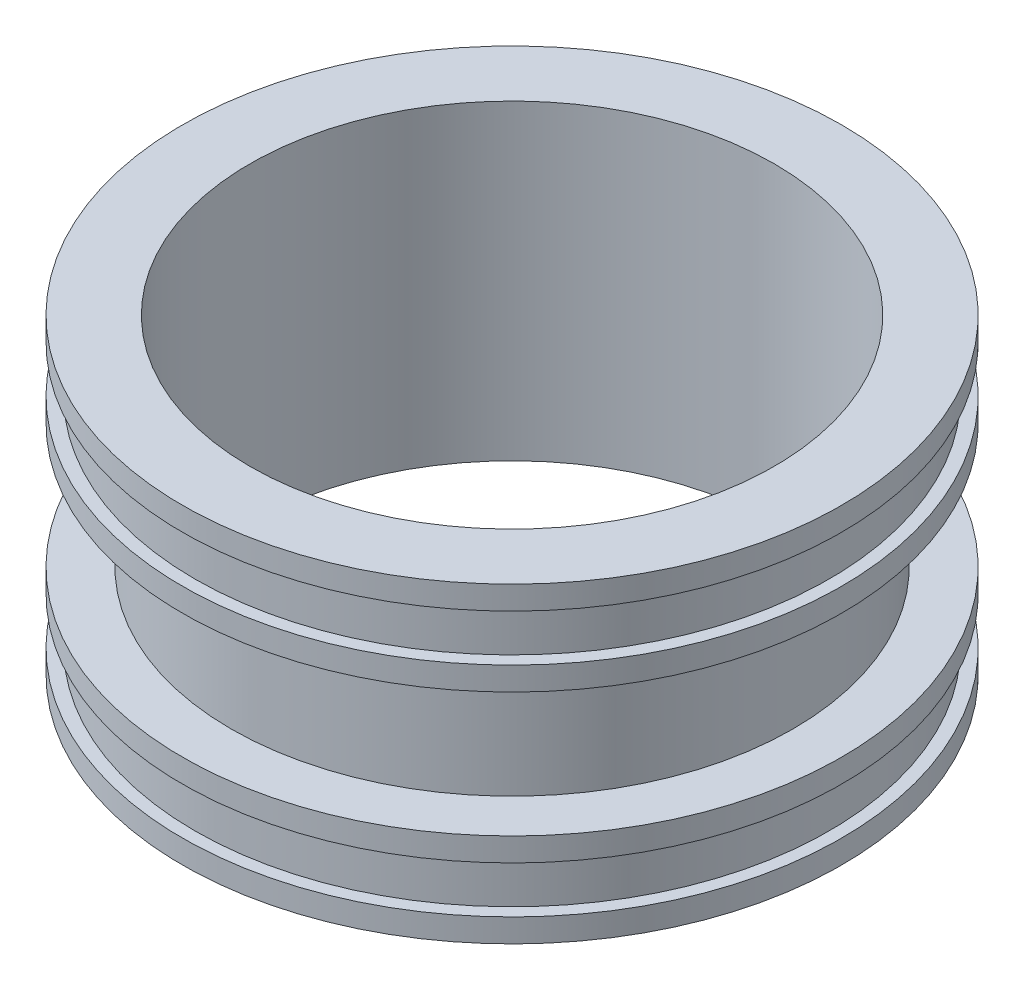
SolidWorks part; units mm, degrees
material "AISI 1020"
ref_plane "Plano frontal" through (0, 0, 0) normal (0, 0, 1) x (1, 0, 0)
ref_plane "Plano superior" through (0, 0, 0) normal (0, 1, 0) x (1, 0, 0)
ref_plane "Plano direito" through (0, 0, 0) normal (1, 0, 0) x (0, 0, -1)
sketch "Esboço1" plane through (0, 0, 0) normal (0, 0, 1) x (1, 0, 0)
  line L0 (0, 0) -> (0, 327.1613) construction
  line L1 (0, 0) -> (502.3995, 0) construction
  line L2 (84.14, 100) -> (105.78, 100)
  line L3 (105.78, 100) -> (105.78, 92.5)
  line L4 (105.78, 70) -> (90.14, 70)
  line L5 (90.14, 70) -> (90.14, 30)
  line L6 (90.14, 30) -> (105.78, 30)
  line L7 (105.78, 30) -> (105.78, 22.5)
  line L8 (105.78, 0) -> (84.14, 0)
  line L9 (84.14, 0) -> (84.14, 100)
  line L10 (105.78, 92.5) -> (101.78, 92.5)
  line L11 (101.78, 92.5) -> (101.78, 77.5)
  line L12 (101.78, 77.5) -> (105.78, 77.5)
  line L13 (84.14, 50) -> (105.78, 50) construction
  line L14 (105.78, 77.5) -> (105.78, 70)
  line L15 (101.78, 22.5) -> (105.78, 22.5)
  line L16 (101.78, 7.5) -> (101.78, 22.5)
  line L17 (105.78, 7.5) -> (101.78, 7.5)
  line L18 (105.78, 7.5) -> (105.78, 0)
  point P22 (90.14, 50)
  dimension "D1" = 168.28
  dimension "D2" = 4
  dimension "D3" = 15
  dimension "D4" = 30
  dimension "250" = 211.56
  dimension "D6" = 6
  dimension "D7" = 100
revolve "Revolução1" add sketch "Esboço1" angle 360 about L0
